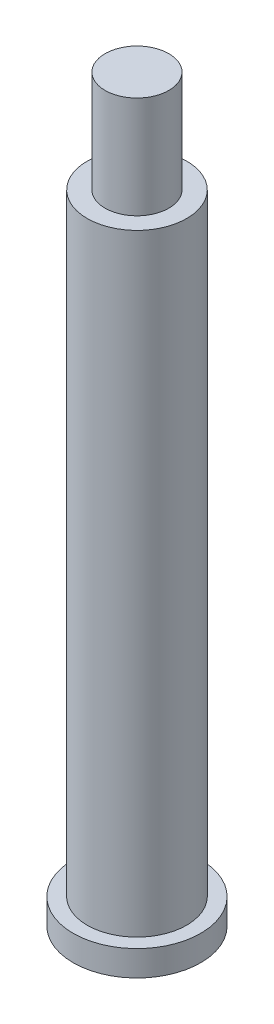
SolidWorks part; units mm, degrees
ref_plane "Front Plane" through (0, 0, 0) normal (0, 0, 1) x (1, 0, 0)
ref_plane "Top Plane" through (0, 0, 0) normal (0, 1, 0) x (1, 0, 0)
ref_plane "Right Plane" through (0, 0, 0) normal (1, 0, 0) x (0, 0, -1)
sketch "Sketch1" plane through (0, 0, 0) normal (0, 1, 0) x (1, 0, 0)
  circle A0 centre (0, 0) radius 5
  dimension "D1" = 10
extrude "Boss-Extrude1" add sketch "Sketch1" along normal blind 2
sketch "Sketch2" plane through (0, 2, 0) normal (0, 1, 0) x (1, 0, 0)
  circle A0 centre (0, 0) radius 3.9
  dimension "D1" = 7.8
extrude "Boss-Extrude2" add sketch "Sketch2" along normal blind 48
sketch "Sketch3" plane through (0, 50, 0) normal (0, 1, 0) x (1, 0, 0)
  circle A0 centre (0, 0) radius 2.5
  dimension "D1" = 5
extrude "Boss-Extrude3" add sketch "Sketch3" along normal blind 8
